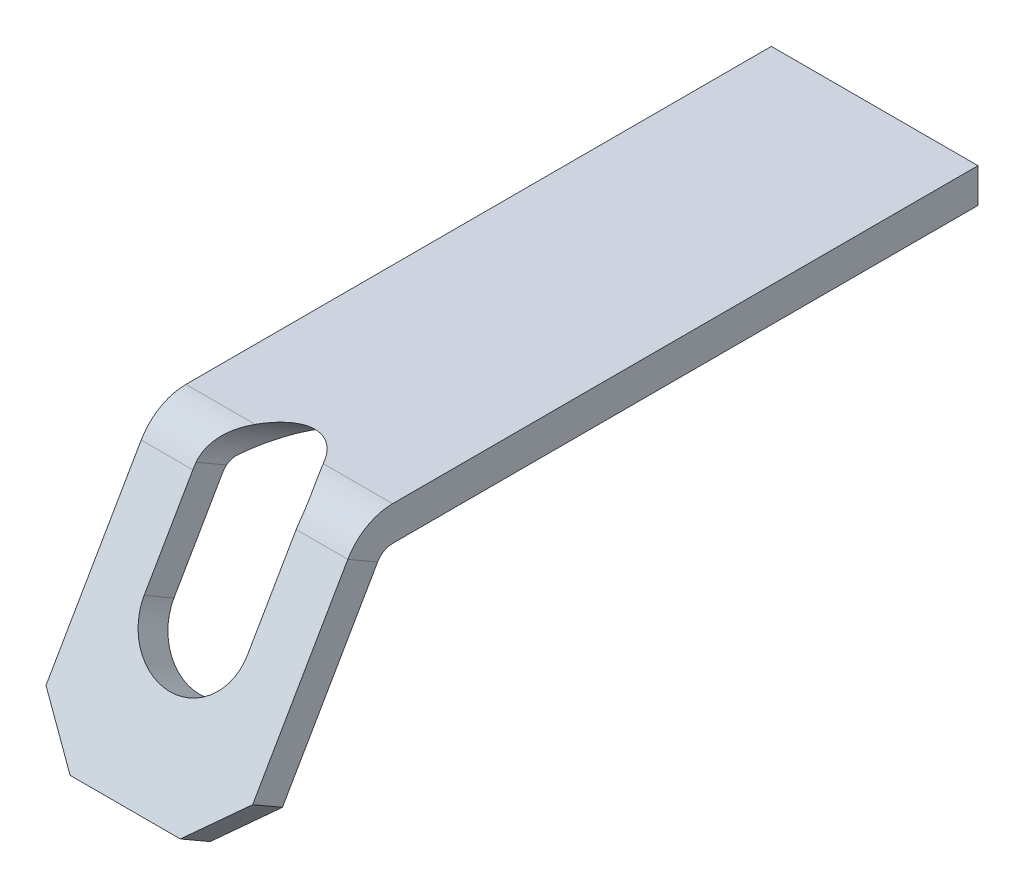
SolidWorks part; units mm, degrees
material "Brass"
ref_plane "Front Plane" through (0, 0, 0) normal (0, 0, 1) x (1, 0, 0)
ref_plane "Top Plane" through (0, 0, 0) normal (0, 1, 0) x (1, 0, 0)
ref_plane "Right Plane" through (0, 0, 0) normal (1, 0, 0) x (0, 0, -1)
sketch "Sketch1" plane through (0, 0, 0) normal (0, 1, 0) x (1, 0, 0)
  line L1 (-1.5, 4.25) -> (1.5, 4.25)
  line L2 (-1.5, 4.25) -> (-1.5, -4.25)
  line L3 (-1.5, -4.25) -> (1.5, -4.25)
  line L4 (1.5, 4.25) -> (1.5, -4.25)
  line L5 (-1.5, 4.25) -> (1.5, -4.25) construction
  line L6 (-1.5, -4.25) -> (1.5, 4.25) construction
  point P0 (0, 0)
  dimension "D1" = 8.5
  dimension "D2" = 3
extrude "Boss-Extrude1" add sketch "Sketch1" along normal mid plane 0.5
sketch "Sketch4" plane through (0, 0, 4.25) normal (0, 0, 1) x (1, 0, 0)
  line L4 (-1.5, -0.25) -> (1.5, -0.25)
  line L5 (1.5, -0.25) -> (1.5, 0.25)
  line L6 (1.5, 0.25) -> (-1.5, 0.25)
  line L7 (-1.5, 0.25) -> (-1.5, -0.25)
  line L8 (-1.5, -0.25) -> (1.5, -0.25)
  line L9 (1.5, -0.25) -> (1.5, 0.25)
  line L10 (1.5, 0.25) -> (-1.5, 0.25)
  line L11 (-1.5, 0.25) -> (-1.5, -0.25)
  dimension "D1" = 0
sketch "Sketch5" plane through (0, 0, 0) normal (1, 0, 0) x (0, 0, -1)
  line L0 (-4.683, -0.25) -> (-6.4151, -3.25)
  line L1 (-4.25, 0.25) -> (-4.25, -0.25) construction
  line L2 (-4.683, -0.25) -> (-4.25, -0.25) construction
  line L3 (-4.25, 0.25) -> (4.25, 0.25) construction
  arc A0 (-4.25, 0) -> (-4.683, -0.25) centre (-4.25, -0.5) ccw
  dimension "D1" = 0.5
  dimension "D2" = 0.5
  dimension "D3" = 30
  dimension "D4" = 3
  dimension "D5" = 3.5
sweep "Sweep1" add profiles "Sketch4" path "Sketch5"
sketch "Sketch6" plane through (0, 2.0903, 3.6205) normal (0, 0.5, 0.866) x (1, 0, 0)
  line L0 (0, -2.4721) -> (0, -3.9721) construction
  line L1 (0.75, -2.4721) -> (0.75, -3.9721)
  line L2 (-0.75, -2.4721) -> (-0.75, -3.9721)
  line L3 (0, -6.0221) -> (0, -4.7221) construction
  line L4 (1.5, -6.0221) -> (-1.5, -6.0221) construction
  arc A0 (0.75, -2.4721) -> (-0.75, -2.4721) centre (0, -2.4721) ccw
  arc A1 (-0.75, -3.9721) -> (0.75, -3.9721) centre (0, -3.9721) ccw
  point P3 (0, -3.2221)
  dimension "D2" = 0.75
  dimension "D1" = 1.5
  dimension "D3" = 1.3
extrude "Cut-Extrude1" cut sketch "Sketch6" against normal through all
chamfer "Chamfer1" distance 0.7 angle 45 2 edges at (1.5, -3.25, 6.4151) (-1.5, -3.25, 6.4151)
